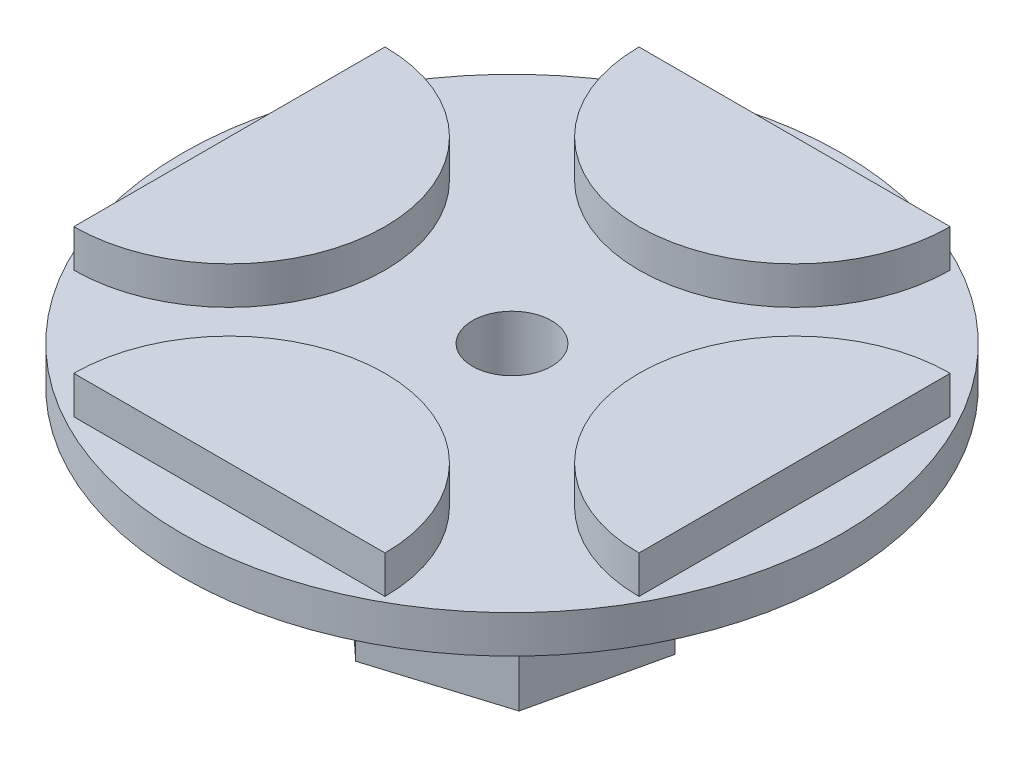
SolidWorks part; units mm, degrees
ref_plane "Front Plane" through (0, 0, 0) normal (0, 0, 1) x (1, 0, 0)
ref_plane "Top Plane" through (0, 0, 0) normal (0, 1, 0) x (1, 0, 0)
ref_plane "Right Plane" through (0, 0, 0) normal (1, 0, 0) x (0, 0, -1)
sketch "Sketch4" plane through (0, 0, 0) normal (0, 1, 0) x (1, 0, 0)
  circle A0 centre (0, 0) radius 17.5
  dimension "D1" = 35
sketch "Sketch1" plane through (0, 0, 0) normal (0, 1, 0) x (1, 0, 0)
  line L0 (0, 0) -> (0, 15) construction
  line L1 (-8.26, 15) -> (8.26, 15)
  line L2 (15, 8.26) -> (15, -8.26)
  line L3 (8.26, -15) -> (-8.26, -15)
  line L4 (-15, -8.26) -> (-15, 8.26)
  arc A0 (-8.26, 15) -> (8.26, 15) centre (0, 15) ccw
  arc A1 (15, 8.26) -> (15, -8.26) centre (15, 0) ccw
  arc A2 (8.26, -15) -> (-8.26, -15) centre (0, -15) ccw
  arc A3 (-15, -8.26) -> (-15, 8.26) centre (-15, 0) ccw
  dimension "D2" = 16.52
  dimension "D1" = 15
  dimension "D3" = 4
extrude "Boss-Extrude1" add sketch "Sketch4" along normal blind 2
extrude "Boss-Extrude2" add sketch "Sketch1" along normal blind 4
sketch "Sketch5" plane through (0, 0, 0) normal (0, -1, 0) x (1, 0, 0)
  line L1 (-6.6198, 2.0442) -> (-5.0802, -4.7108)
  line L2 (-5.0802, -4.7108) -> (1.5396, -6.755)
  line L3 (1.5396, -6.755) -> (6.6198, -2.0442)
  line L4 (6.6198, -2.0442) -> (5.0802, 4.7108)
  line L5 (5.0802, 4.7108) -> (-1.5396, 6.755)
  line L6 (-1.5396, 6.755) -> (-6.6198, 2.0442)
  circle A1 centre (0, 0) radius 6 construction
  point P1 (0, 0)
  dimension "D1" = 12
extrude "Boss-Extrude3" add sketch "Sketch5" along normal blind 10
sketch "Sketch6" plane through (0, 2, 0) normal (0, 1, 0) x (1, 0, 0)
  circle A0 centre (0, 0) radius 2.1
  dimension "D1" = 4.2
extrude "Cut-Extrude1" cut sketch "Sketch6" against normal through all both and the other way through all
